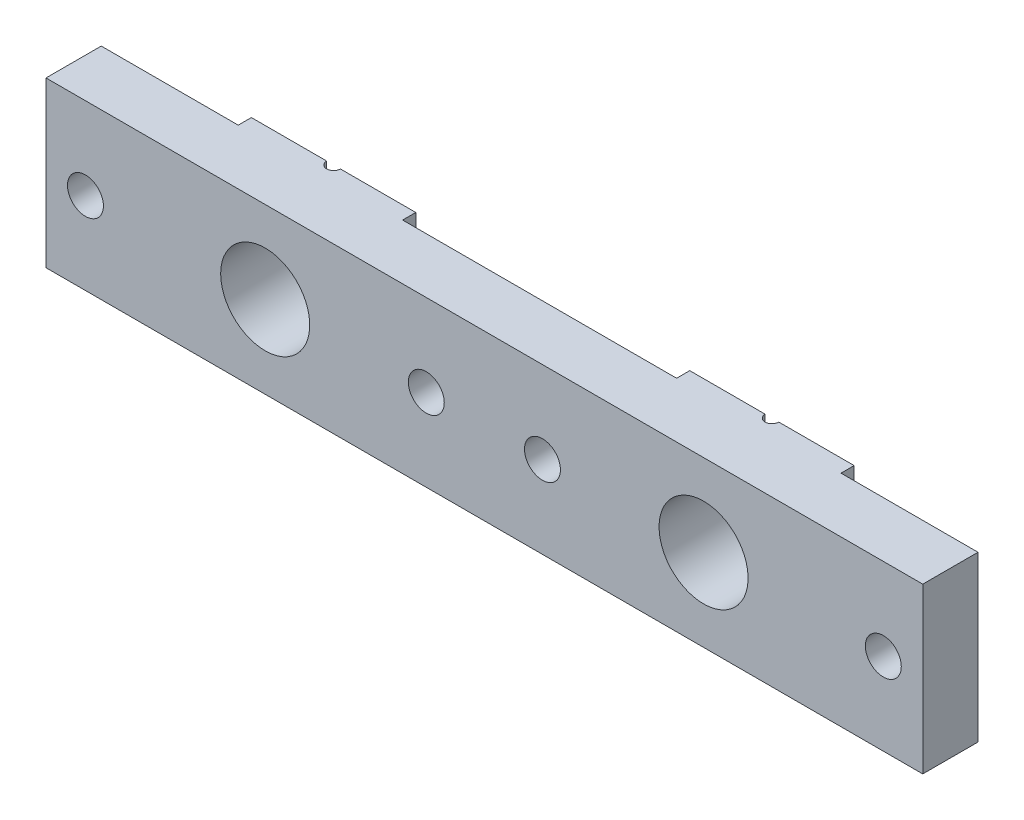
SolidWorks part; units mm, degrees
material "6061-T6 Al"
ref_plane "Front Plane" through (0, 0, 0) normal (0, 0, 1) x (1, 0, 0)
ref_plane "Top Plane" through (0, 0, 0) normal (0, 1, 0) x (1, 0, 0)
ref_plane "Right Plane" through (0, 0, 0) normal (1, 0, 0) x (0, 0, -1)
sketch "Sketch1" plane through (0, 0, 0) normal (0, 0, 1) x (1, 0, 0)
  line L0 (0, 0) -> (0, -9.525) construction
  line L1 (-50.8, 9.525) -> (50.8, 9.525)
  line L2 (-50.8, 9.525) -> (-50.8, -9.525)
  line L3 (-50.8, -9.525) -> (50.8, -9.525)
  line L4 (50.8, 9.525) -> (50.8, -9.525)
  line L6 (0, 0) -> (50.8, 0) construction
  dimension "D1" = 101.6
  dimension "D2" = 19.05
extrude "Extrude1" add sketch "Sketch1" along normal blind 7.9248
hole_wizard "13/32 (0.40625) Diameter Hole1" positions "Sketch3" profile "Sketch4" hole size "13/32" standard "Ansi Inch" end condition through all
sketch "Sketch3" plane through (0, 0, 0) normal (0, 0, -1) x (-1, 0, 0)
  line L0 (25.4, 0) -> (-25.4, 0) construction
  line L3 (55, 0) -> (-55, 0) construction
  point P0 (25.4, 0)
  point P1 (-25.4, 0)
  dimension "D1" = 50.8
  dimension "D2" = 25.4
sketch "Sketch4" plane through (-25.4, 0, 0) normal (1, 0, 0) x (0, 1, 0)
  line L0 (0, 0) -> (0, 7.9248)
  line L1 (0, 7.9248) -> (5.1594, 7.9248)
  line L2 (5.1594, 7.9248) -> (5.1594, 0)
  line L5 (5.1594, 0) -> (0, 0)
  line L11 (0, -6.35) -> (0, 107.95) construction
  dimension "Thru Hole Dia." = 10.3187
  dimension "Thru Hole Depth" = 7.9248
hole_wizard "#8-32 Tapped Hole1" positions "Sketch7" profile "Sketch6" tap size "#8-32" standard "Ansi Inch" end condition through all
sketch "Sketch7" plane through (0, 0, 7.9248) normal (0, 0, 1) x (1, 0, 0)
  line L0 (-46.228, 0) -> (-6.731, 0) construction
  line L1 (-6.731, 0) -> (6.731, 0) construction
  line L2 (6.731, 0) -> (46.228, 0) construction
  line L3 (55, 0) -> (-55, 0) construction
  circle A0 centre (-25.4, 0) radius 5.1594 construction
  circle A1 centre (25.4, 0) radius 5.1594 construction
  point P0 (-46.228, 0)
  point P1 (-6.731, 0)
  point P3 (6.731, 0)
  point P5 (46.228, 0)
  dimension "D3" = 18.669
  dimension "D4" = 20.828
  dimension "D1" = 20.828
  dimension "D2" = 18.669
sketch "Sketch6" plane through (-46.228, 0, 7.9248) normal (1, 0, 0) x (0, -1, 0)
  line L0 (0, 0) -> (0, 7.9248)
  line L1 (0, 7.9248) -> (2.0828, 7.9248)
  line L2 (2.0828, 7.9248) -> (2.0828, 0)
  line L5 (2.0828, 0) -> (0, 0)
  line L11 (0, -6.35) -> (0, 107.95) construction
  dimension "Thread Major Dia." = 4.1656
  dimension "Thru Tap Drill Depth" = 7.9248
sketch "Sketch9" plane through (0, 0, 0) normal (0, 0, -1) x (-1, 0, 0)
  line L0 (50.8, -9.525) -> (-50.8, -9.525) construction
  line L1 (-15.875, 9.525) -> (15.875, 9.525)
  line L2 (-15.875, 9.525) -> (-15.875, -9.525)
  line L3 (-15.875, -9.525) -> (15.875, -9.525)
  line L4 (15.875, 9.525) -> (15.875, -9.525)
  line L5 (-50.8, 9.525) -> (50.8, 9.525) construction
  line L6 (50.8, 9.525) -> (50.8, -9.525) construction
  line L7 (-50.8, 9.525) -> (-34.925, 9.525)
  line L8 (-50.8, 9.525) -> (-50.8, -9.525)
  line L9 (-50.8, -9.525) -> (-34.925, -9.525)
  line L10 (-34.925, 9.525) -> (-34.925, -9.525)
  line L11 (34.925, 9.525) -> (50.8, 9.525)
  line L12 (34.925, 9.525) -> (34.925, -9.525)
  line L13 (34.925, -9.525) -> (50.8, -9.525)
  line L14 (50.8, 9.525) -> (50.8, -9.525)
  line L15 (-50.8, -9.525) -> (-50.8, 9.525) construction
  circle A0 centre (-25.4, 0) radius 5.1594 construction
  circle A1 centre (25.4, 0) radius 5.1594 construction
  dimension "D1" = 9.525
  dimension "D2" = 9.525
  dimension "D3" = 9.525
  dimension "D4" = 9.525
extrude "Extrude3" cut sketch "Sketch9" against normal blind 1.524
hole_wizard "1/16 (0.0625) Diameter Hole1" positions "Sketch12" profile "Sketch13" hole size "1/16" standard "Ansi Inch" end condition through all
sketch "Sketch12" plane through (0, 9.525, 0) normal (0, 1, 0) x (-1, 0, 0)
  line L0 (-34.925, 0) -> (-15.875, 0) construction
  line L1 (15.875, 0) -> (34.925, 0) construction
  point P0 (-25.4, 0)
  point P1 (25.4, 0)
sketch "Sketch13" plane through (25.4, 9.525, 0) normal (1, 0, 0) x (0, 0, 1)
  line L0 (0, 0) -> (0, 19.05)
  line L1 (0, 19.05) -> (0.7937, 19.05)
  line L2 (0.7937, 19.05) -> (0.7937, 0)
  line L5 (0.7937, 0) -> (0, 0)
  line L11 (0, -6.35) -> (0, 107.95) construction
  dimension "Thru Hole Dia." = 1.5875
  dimension "Thru Hole Depth" = 19.05
